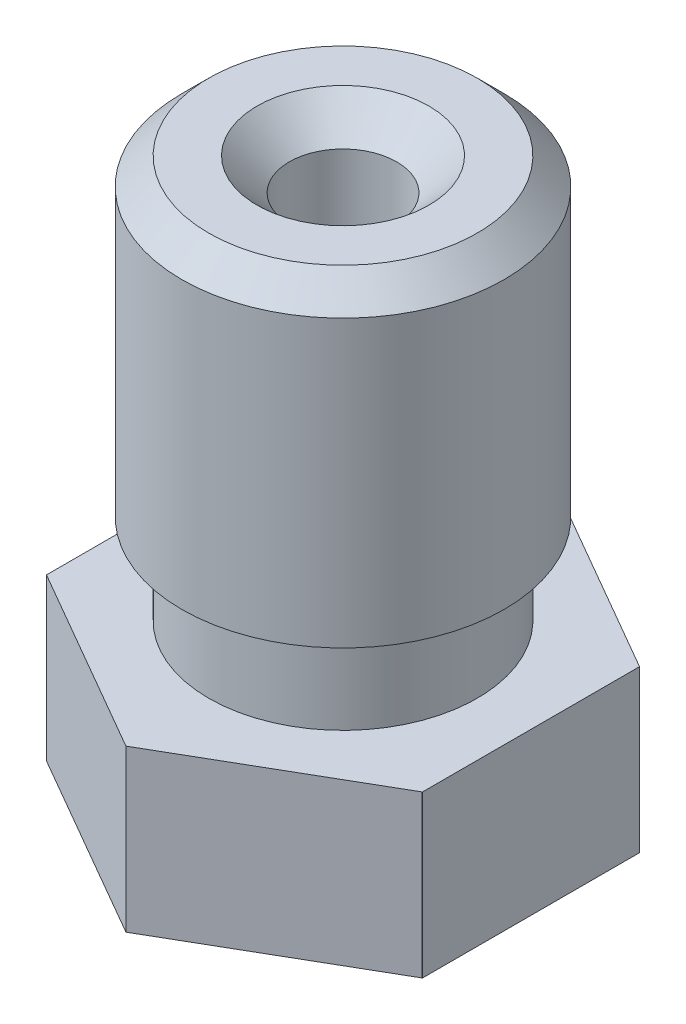
SolidWorks part; units mm, degrees
ref_plane "Спереди" through (0, 0, 0) normal (0, 0, 1) x (1, 0, 0)
ref_plane "Сверху" through (0, 0, 0) normal (0, 1, 0) x (1, 0, 0)
ref_plane "Справа" through (0, 0, 0) normal (1, 0, 0) x (0, 0, -1)
sketch "Эскиз1" plane through (0, 0, 0) normal (1, 0, 0) x (0, 0, -1)
  line L0 (0, 0) -> (0, 154.7371) construction
  line L1 (-0.4, 0.8) -> (-0.4, 0)
  line L2 (-0.4, 0) -> (-0.5, 0)
  line L3 (-0.5, 0) -> (-1.9004, 2)
  line L4 (-1.9004, 2) -> (-4.04, 2)
  line L5 (-4.04, 2) -> (-4.04, 5)
  line L6 (-4.04, 5) -> (-2.5, 5)
  line L7 (-2.5, 5) -> (-2.5, 6.5)
  line L8 (-2.5, 6.5) -> (-3, 6.682)
  line L9 (-3, 6.682) -> (-3, 12)
  line L10 (-3, 12) -> (-2.5, 12.5)
  line L11 (-2.5, 12.5) -> (-1, 12.5)
  line L12 (-0.4, 0.8) -> (-0.75, 1.0103)
  line L13 (-0.75, 1.0103) -> (-0.75, 1.8498)
  line L14 (-0.75, 1.8498) -> (-1, 2)
  line L15 (-1, 2) -> (-1, 12.5)
  dimension "D10" = 0.8
  dimension "D1" = 0.4
  dimension "D2" = 1
  dimension "D3" = 125
  dimension "D4" = 10.5
  dimension "D5" = 6
  dimension "D6" = 6
  dimension "D7" = 5
  dimension "D8" = 70
  dimension "D9" = 45
  dimension "D11" = 59
  dimension "D12" = 8.08
  dimension "D13" = 7.5
  dimension "D14" = 12.5
  dimension "D15" = 1.5
  dimension "D16" = 2
  dimension "D17" = 10.5
revolve "Повернуть1" add sketch "Эскиз1" angle 360 about L0
cosmetic thread "Условное изображение резьбы1" parameters "D2"=4.891
sketch "Эскиз2" plane through (0, 2, 0) normal (0, -1, 0) x (1, 0, 0)
  line L1 (0, 4.0415) -> (-3.5, 2.0207)
  line L2 (-3.5, 2.0207) -> (-3.5, -2.0207)
  line L3 (-3.5, -2.0207) -> (0, -4.0415)
  line L4 (0, -4.0415) -> (3.5, -2.0207)
  line L5 (3.5, -2.0207) -> (3.5, 2.0207)
  line L6 (3.5, 2.0207) -> (0, 4.0415)
  circle A0 centre (0, 0) radius 3.5 construction
  dimension "D1" = 7
extrude "Вырез-Вытянуть1" cut sketch "Эскиз2" against normal up to surface (3 mm away) flip side to cut up to face at (0, 5, -4.04)
chamfer "Фаска1" distance 0.6 angle 45 1 edges at (0, 12.5, -1)
